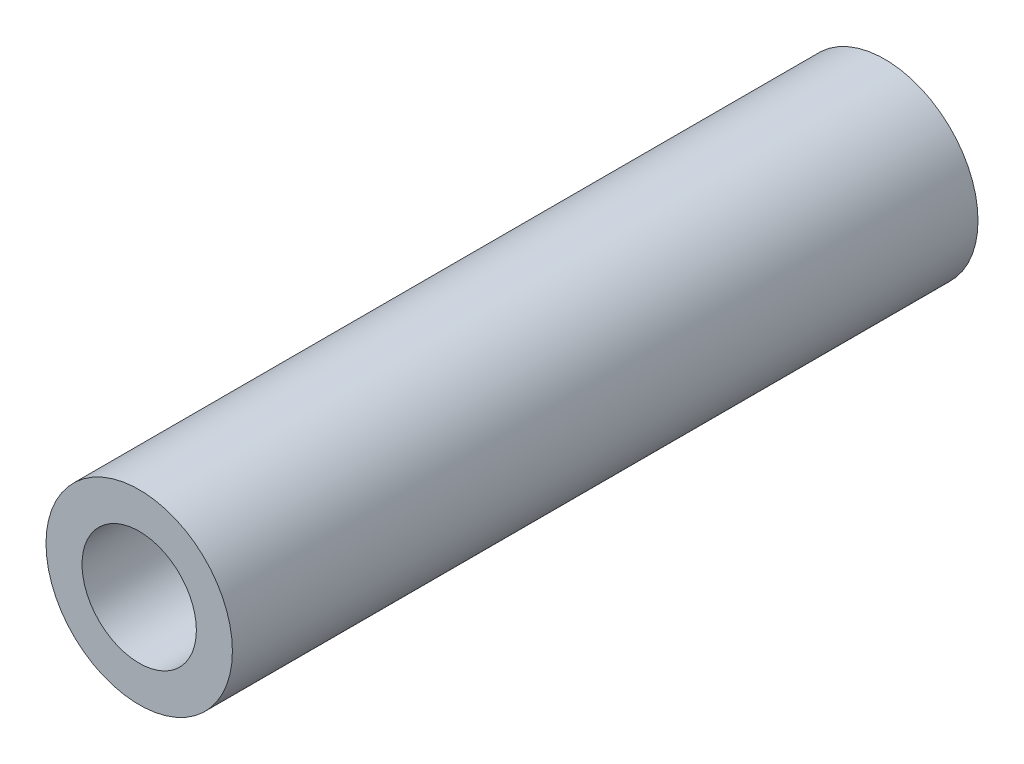
SolidWorks part; units mm, degrees
ref_plane "Front Plane" through (0, 0, 0) normal (0, 0, 1) x (1, 0, 0)
ref_plane "Top Plane" through (0, 0, 0) normal (0, 1, 0) x (1, 0, 0)
ref_plane "Right Plane" through (0, 0, 0) normal (1, 0, 0) x (0, 0, -1)
sketch "Sketch1" plane through (0, 0, 0) normal (0, 0, 1) x (1, 0, 0)
  circle A0 centre (0, 0) radius 2.3812
  circle A1 centre (0, 0) radius 1.4605
  dimension "OD" = 4.7625
  dimension "ID" = 2.921
extrude "Extrude1" add sketch "Sketch1" along normal mid plane 19.05
sketch "Sketch2" plane through (0, 0, 0) normal (1, 0, 0) x (0, 0, -1)
  line L0 (-9.525, -1.4605) -> (9.525, -1.4605) construction
  line L3 (9.525, 1.4605) -> (-9.525, 1.4605) construction
  line L5 (-9.525, -1.4605) -> (9.525, -1.4605)
  line L6 (9.525, 1.4605) -> (-9.525, 1.4605)
sketch "Sketch4" plane through (0, 0, 9.525) normal (0, 0, 1) x (1, 0, 0)
  line L0 (0, 0) -> (-1.0327, 1.0327)
  line L1 (0, -2.6194) -> (0, 2.6194) construction
  circle A0 centre (0, 0) radius 1.4605 construction
  dimension "D1" = 45
